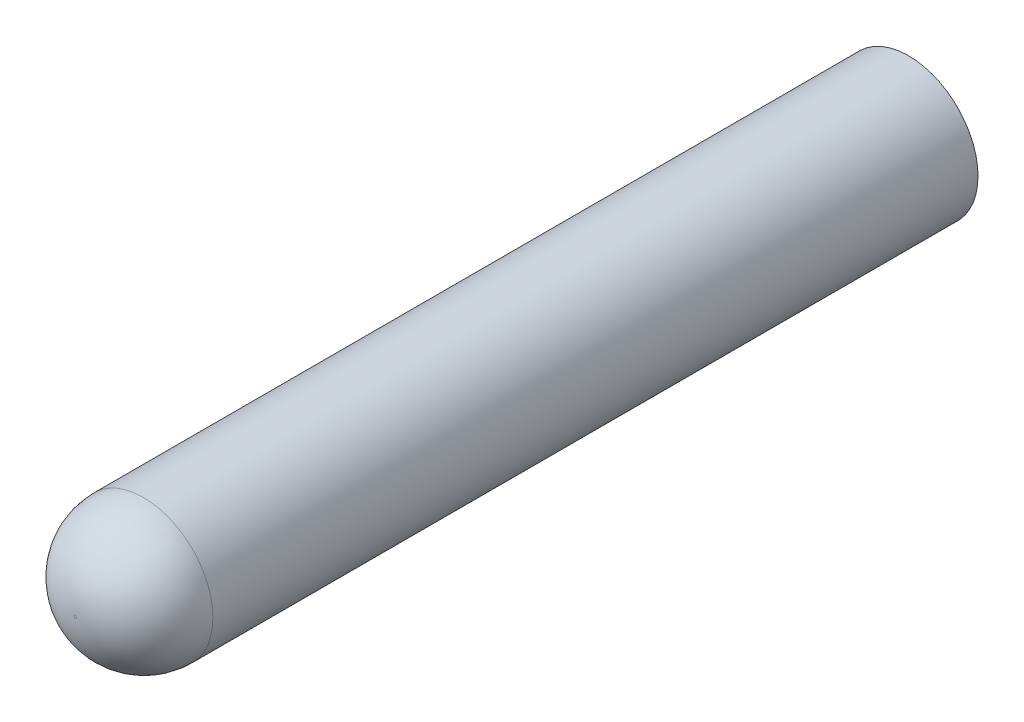
SolidWorks part; units mm, degrees
ref_plane "Front Plane" through (0, 0, 0) normal (0, 0, 1) x (1, 0, 0)
ref_plane "Top Plane" through (0, 0, 0) normal (0, 1, 0) x (1, 0, 0)
ref_plane "Right Plane" through (0, 0, 0) normal (1, 0, 0) x (0, 0, -1)
sketch "Sketch1" plane through (0, 0, 0) normal (0, 0, 1) x (1, 0, 0)
  circle A0 centre (0, 0) radius 0.5
extrude "Boss-Extrude1" add sketch "Sketch1" along normal blind 6
fillet "Fillet1" radius 0.49 1 edges at (0.5, 0, 6)
